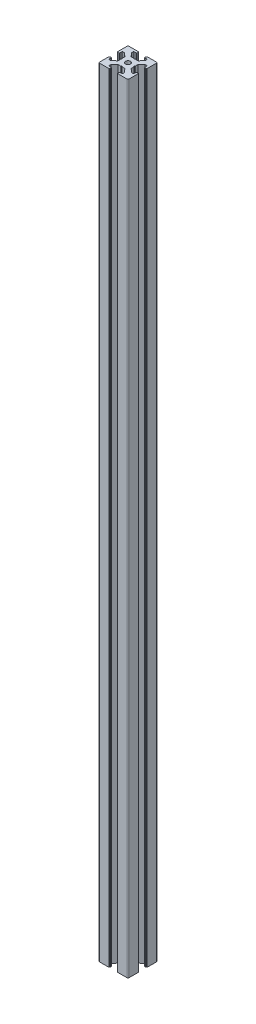
SolidWorks part; units mm, degrees
ref_plane "Front Plane" through (0, 0, 0) normal (0, 0, 1) x (1, 0, 0)
ref_plane "Top Plane" through (0, 0, 0) normal (0, 1, 0) x (1, 0, 0)
ref_plane "Right Plane" through (0, 0, 0) normal (1, 0, 0) x (0, 0, -1)
sketch "Sketch3" plane through (0, 0, 0) normal (0, 1, 0) x (1, 0, 0)
  line L0 (11, 30) -> (11, 27.75)
  line L1 (0, 0) -> (30, 0)
  line L2 (0, 0) -> (0, 30)
  line L3 (0, 30) -> (30, 30)
  line L4 (30, 0) -> (30, 30)
  line L5 (11, 27.75) -> (8, 27.75)
  line L6 (8, 27.75) -> (8, 25.5)
  line L7 (8, 25.5) -> (11.5, 21.75)
  line L8 (11.5, 21.75) -> (18.5, 21.75)
  line L9 (18.5, 21.75) -> (22, 25.5)
  line L10 (22, 25.5) -> (22, 27.75)
  line L11 (22, 27.75) -> (19, 27.75)
  line L12 (19, 27.75) -> (19, 30)
  line L13 (19, 30) -> (11, 30)
  line L14 (14.5, 21.75) -> (15, 21.25)
  line L15 (15, 21.25) -> (15.5, 21.75)
  line L16 (15.5, 21.75) -> (14.5, 21.75)
  line L17 (19, 29.5) -> (19, 30)
  line L18 (19.5, 30) -> (19, 30)
  line L19 (11, 29.5) -> (11, 30)
  line L20 (10.5, 30) -> (11, 30)
  line L21 (0, 19) -> (2.25, 19)
  line L22 (2.25, 19) -> (2.25, 22)
  line L23 (2.25, 22) -> (4.5, 22)
  line L24 (4.5, 22) -> (8.25, 18.5)
  line L25 (8.25, 18.5) -> (8.25, 11.5)
  line L26 (8.25, 11.5) -> (4.5, 8)
  line L27 (4.5, 8) -> (2.25, 8)
  line L28 (2.25, 8) -> (2.25, 11)
  line L29 (2.25, 11) -> (0, 11)
  line L30 (0, 11) -> (0, 19)
  line L31 (8.25, 15.5) -> (8.25, 14.5)
  line L32 (8.25, 14.5) -> (8.75, 15)
  line L33 (8.75, 15) -> (8.25, 15.5)
  line L34 (0.5, 19) -> (0, 19)
  line L35 (0, 19.5) -> (0, 19)
  line L36 (0, 10.5) -> (0, 11)
  line L37 (0.5, 11) -> (0, 11)
  line L38 (15, 30) -> (15, 0) construction
  line L39 (30, 15) -> (0, 15) construction
  line L40 (15, 8.75) -> (15.5, 8.25)
  line L41 (14.5, 8.25) -> (15, 8.75)
  line L42 (15.5, 8.25) -> (14.5, 8.25)
  line L43 (19.5, 0) -> (19, 0)
  line L44 (19, 0.5) -> (19, 0)
  line L45 (10.5, 0) -> (11, 0)
  line L46 (11, 0.5) -> (11, 0)
  line L47 (19, 2.25) -> (19, 0)
  line L48 (22, 2.25) -> (19, 2.25)
  line L49 (22, 4.5) -> (22, 2.25)
  line L50 (18.5, 8.25) -> (22, 4.5)
  line L51 (11.5, 8.25) -> (18.5, 8.25)
  line L52 (8, 4.5) -> (11.5, 8.25)
  line L53 (8, 2.25) -> (8, 4.5)
  line L54 (11, 2.25) -> (8, 2.25)
  line L55 (11, 0) -> (11, 2.25)
  line L56 (19, 0) -> (11, 0)
  line L57 (21.75, 14.5) -> (21.25, 15)
  line L58 (21.75, 15.5) -> (21.75, 14.5)
  line L59 (21.25, 15) -> (21.75, 15.5)
  line L60 (29.5, 11) -> (30, 11)
  line L61 (30, 10.5) -> (30, 11)
  line L62 (30, 19.5) -> (30, 19)
  line L63 (29.5, 19) -> (30, 19)
  line L64 (27.75, 11) -> (30, 11)
  line L65 (27.75, 8) -> (27.75, 11)
  line L66 (25.5, 8) -> (27.75, 8)
  line L67 (21.75, 11.5) -> (25.5, 8)
  line L68 (21.75, 18.5) -> (21.75, 11.5)
  line L69 (25.5, 22) -> (21.75, 18.5)
  line L70 (27.75, 22) -> (25.5, 22)
  line L71 (27.75, 19) -> (27.75, 22)
  line L72 (30, 19) -> (27.75, 19)
  line L73 (30, 11) -> (30, 19)
  arc A0 (19.5, 30) -> (19, 29.5) centre (19, 30) cw
  arc A1 (10.5, 30) -> (11, 29.5) centre (11, 30) ccw
  arc A2 (0.5, 19) -> (0, 19.5) centre (0, 19) ccw
  arc A3 (0.5, 11) -> (0, 10.5) centre (0, 11) cw
  arc A4 (19.5, 0) -> (19, 0.5) centre (19, 0) ccw
  arc A5 (10.5, 0) -> (11, 0.5) centre (11, 0) cw
  arc A6 (29.5, 11) -> (30, 10.5) centre (30, 11) ccw
  arc A7 (29.5, 19) -> (30, 19.5) centre (30, 19) cw
  point P7 (15, 21.75)
  point P16 (15, 30)
  point P26 (8.25, 15)
  point P35 (0, 15)
  dimension "D16" = 0.5
  dimension "D17" = 0.5
  dimension "D28" = 0.5
  dimension "D29" = 0.5
  dimension "D1" = 30
  dimension "D2" = 30
  dimension "D3" = 11
  dimension "D4" = 11
  dimension "D5" = 2.25
  dimension "D6" = 2.25
  dimension "D7" = 3
  dimension "D8" = 3
  dimension "D9" = 2.25
  dimension "D10" = 2.25
  dimension "D11" = 7
  dimension "D12" = 8.25
  dimension "D13" = 0.5
  dimension "D14" = 0.5
  dimension "D15" = 0.5
  dimension "D18" = 11
  dimension "D19" = 11
  dimension "D20" = 2.25
  dimension "D21" = 2.25
  dimension "D22" = 3
  dimension "D23" = 7
  dimension "D24" = 8.25
  dimension "D25" = 0.5
  dimension "D26" = 0.5
  dimension "D27" = 0.5
extrude "Boss-Extrude1" add sketch "Sketch3" along normal blind 795 contours L72 A7 L4 L3 A0 L12 L11 L10 L9 L8 L15 L14 L7 L6 L5 L0 A1 L2 A2 L21 L22 L23 L24 L25 L33 L32 L26 L27 L28 L29 A3 L1 A5 L55 L54 L53 L52 L51 L41 L40 L50 L49 L48 L47 A4
fillet "Fillet1" radius 1 4 edges at (0, 397.5, 0) (30, 397.5, 0) (30, 397.5, -30) (0, 397.5, -30)
sketch "Sketch4" plane through (0, 795, 0) normal (0, 1, 0) x (1, 0, 0)
  line L0 (18.5, 21.75) -> (8.25, 11.5) construction
  line L1 (21.75, 18.5) -> (11.5, 8.25) construction
  line L2 (15.5, 21.75) -> (21.75, 15.5) construction
  line L9 (8.25, 14.5) -> (14.5, 8.25) construction
  line L10 (8.25, 15.5) -> (14.5, 21.75) construction
  line L11 (21.75, 14.5) -> (15.5, 8.25) construction
  line L12 (11.5, 21.75) -> (21.75, 11.5) construction
  line L13 (8.25, 18.5) -> (18.5, 8.25) construction
  line L20 (30, 15) -> (0, 15) construction
  circle A0 centre (15, 15) radius 2.5
  dimension "D1" = 5
extrude "Cut-Extrude1" cut sketch "Sketch4" against normal through all
fillet "Fillet2" radius 0.5 24 edges at (2.25, 397.5, -22) (2.25, 397.5, -19) (8.25, 397.5, -15.5) (8.25, 397.5, -14.5) (2.25, 397.5, -11) (2.25, 397.5, -8) (8, 397.5, -2.25) (11, 397.5, -2.25) (14.5, 397.5, -8.25) (15.5, 397.5, -8.25) (19, 397.5, -2.25) (22, 397.5, -2.25) (27.75, 397.5, -8) (27.75, 397.5, -11) (27.75, 397.5, -19) (27.75, 397.5, -22) (21.75, 397.5, -14.5) (21.75, 397.5, -15.5) (15.5, 397.5, -21.75) (14.5, 397.5, -21.75) (22, 397.5, -27.75) (19, 397.5, -27.75) (11, 397.5, -27.75) (8, 397.5, -27.75)
